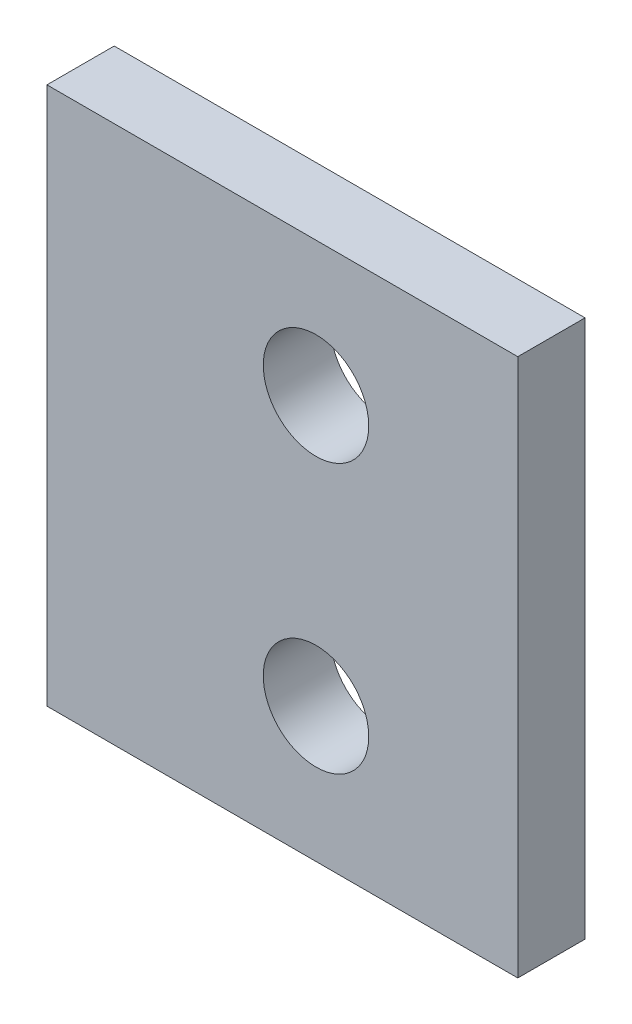
SolidWorks part; units mm, degrees
ref_plane "Front Plane" through (0, 0, 0) normal (0, 0, 1) x (1, 0, 0)
ref_plane "Top Plane" through (0, 0, 0) normal (0, 1, 0) x (1, 0, 0)
ref_plane "Right Plane" through (0, 0, 0) normal (1, 0, 0) x (0, 0, -1)
sketch "Sketch1" plane through (0, 0, 0) normal (0, 0, 1) x (1, 0, 0)
  line L1 (-3.175, 101.6) -> (-25.4, 101.6)
  line L2 (-3.175, 101.6) -> (-3.175, 76.2)
  line L3 (-3.175, 76.2) -> (-25.4, 76.2)
  line L4 (-25.4, 101.6) -> (-25.4, 76.2)
  circle A2 centre (-12.7, 82.55) radius 2.4892
  circle A3 centre (-12.7, 95.25) radius 2.4892
  dimension "D1" = 25.4
extrude "Boss-Extrude1" add sketch "Sketch1" along normal blind 3.175
equation "\"Thick\"= \"in\""
